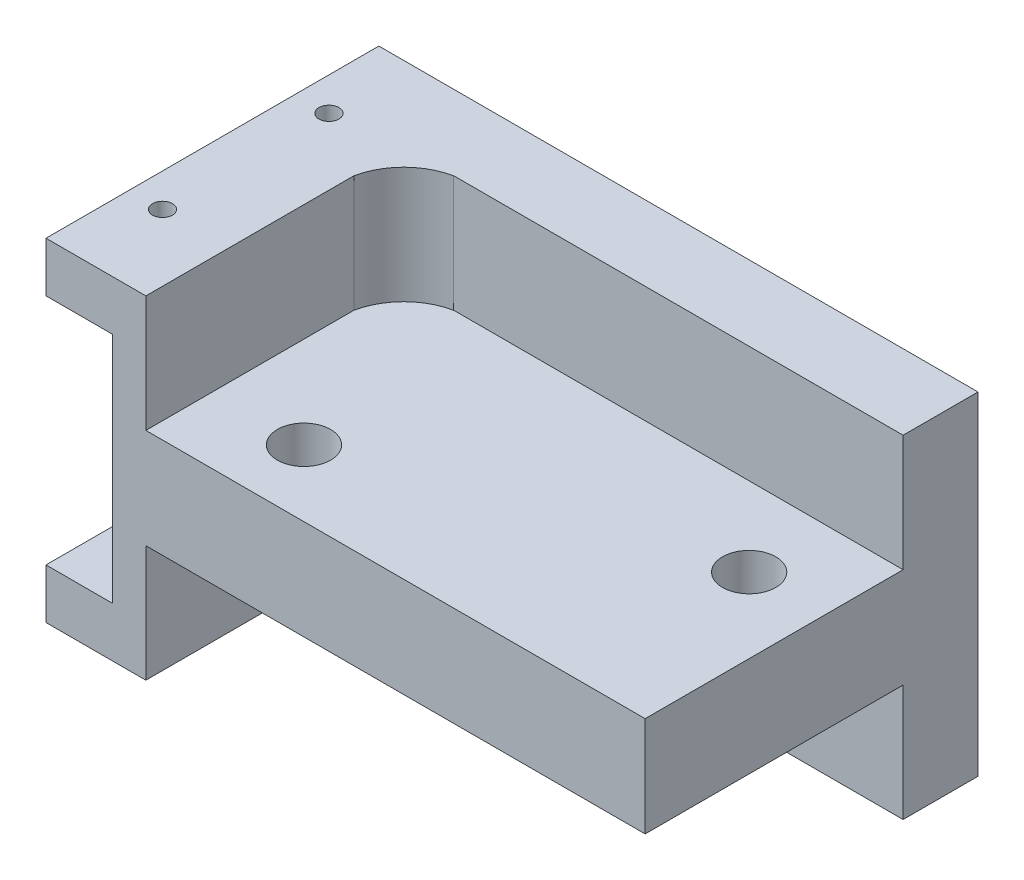
SolidWorks part; units mm, degrees
ref_plane "Front Plane" through (0, 0, 0) normal (0, 0, 1) x (1, 0, 0)
ref_plane "Top Plane" through (0, 0, 0) normal (0, 1, 0) x (1, 0, 0)
ref_plane "Right Plane" through (0, 0, 0) normal (1, 0, 0) x (0, 0, -1)
sketch "Sketch1" plane through (0, 0, 0) normal (0, 1, 0) x (1, 0, 0)
  line L1 (-17.5, -10) -> (17.5, -10)
  line L2 (-17.5, -10) -> (-17.5, 10)
  line L3 (-17.5, 10) -> (17.5, 10)
  line L4 (17.5, -10) -> (17.5, 10)
  point P0 (0, 0)
  dimension "D1" = 20
  dimension "D2" = 35
extrude "Boss-Extrude2" add sketch "Sketch1" along normal mid plane 20
sketch "Sketch4" plane through (0, 10, 0) normal (0, 1, 0) x (1, 0, 0)
  line L0 (-12.5, -10) -> (-12.5, 2.5)
  line L1 (-17.5, -10) -> (17.5, -10) construction
  line L2 (-9.5, 5.5) -> (17.5, 5.5)
  line L3 (17.5, -10) -> (17.5, 10) construction
  line L4 (17.5, 5.5) -> (17.5, -10)
  line L5 (17.5, -10) -> (-12.5, -10)
  line L6 (17.5, -10) -> (17.5, 10) construction
  line L7 (-17.5, -10) -> (17.5, -10) construction
  arc A0 (-12.5, 2.5) -> (-9.5, 5.5) centre (-8.7081, 1.7081) cw
  dimension "D1" = 5
  dimension "D2" = 4.5
extrude "Cut-Extrude1" cut sketch "Sketch4" against normal blind 7
sketch "Sketch6" plane through (0, -10, 0) normal (0, -1, 0) x (1, 0, 0)
  line L0 (-12.5, 10) -> (-12.5, -2.5)
  line L1 (-17.5, 10) -> (17.5, 10) construction
  line L2 (-9.5, -5.5) -> (17.5, -5.5)
  line L3 (17.5, 10) -> (17.5, -10) construction
  line L8 (-12.5, 10) -> (17.5, 10)
  line L9 (17.5, 10) -> (17.5, -5.5)
  arc A0 (-12.5, -2.5) -> (-9.5, -5.5) centre (-9.1347, -2.1347) ccw
extrude "Cut-Extrude2" cut sketch "Sketch6" against normal blind 7
sketch "Sketch8" plane through (0, 3, 0) normal (0, 1, 0) x (1, 0, 0)
  line L0 (-12.5, -10) -> (17.5, -10) construction
  line L1 (-12.5, 2.5) -> (-12.5, -10) construction
  line L2 (17.5, -10) -> (17.5, 5.5) construction
  circle A0 centre (-7, -6) radius 1.6
  circle A1 centre (13, 0.75) radius 1.6
  dimension "D1" = 3.2
  dimension "D2" = 3.2
  dimension "D3" = 4
  dimension "D4" = 5.5
  dimension "D5" = 6.75
  dimension "D6" = 20
  dimension "D7" = 4.5
extrude "Cut-Extrude3" cut sketch "Sketch8" against normal blind 7
sketch "Sketch9" plane through (-17.5, 0, 0) normal (-1, 0, 0) x (0, 0, 1)
  line L0 (-10, 10) -> (-10, -10) construction
  line L1 (-10, 7) -> (10, 7)
  line L2 (-10, 7) -> (-10, -7)
  line L3 (-10, -7) -> (10, -7)
  line L4 (10, 7) -> (10, -7)
  line L5 (10, 10) -> (10, -10) construction
  line L6 (-10, 10) -> (10, 10) construction
  line L7 (-10, -10) -> (10, -10) construction
  dimension "D1" = 3
  dimension "D2" = 3
  dimension "D3" = 14
extrude "Cut-Extrude4" cut sketch "Sketch9" against normal blind 3
sketch "Sketch10" plane through (0, 10, 0) normal (0, 1, 0) x (1, 0, 0)
  line L0 (17.5, 10) -> (-17.5, 10) construction
  line L1 (-17.5, 10) -> (-17.5, -10) construction
  circle A0 centre (-16.5, 5) radius 0.6
  circle A1 centre (-16.5, -5) radius 0.6
  dimension "D1" = 1.2
  dimension "D2" = 1.2
  dimension "D3" = 10
  dimension "D4" = 5
  dimension "D5" = 1
  dimension "D6" = 1
extrude "Cut-Extrude5" cut sketch "Sketch10" against normal blind 3
sketch "Sketch11" plane through (0, -10, 0) normal (0, -1, 0) x (1, 0, 0)
  line L0 (-17.5, -10) -> (-17.5, 10) construction
  line L1 (17.5, -10) -> (-17.5, -10) construction
  circle A0 centre (-16.5, 5) radius 0.6
  circle A1 centre (-16.5, -5) radius 0.6
  dimension "D1" = 1.2
  dimension "D2" = 1.2
  dimension "D3" = 1
  dimension "D4" = 1
  dimension "D5" = 10
  dimension "D6" = 5
extrude "Cut-Extrude6" cut sketch "Sketch11" against normal blind 3
sketch "Sketch12" plane through (-17.5, 0, 0) normal (-1, 0, 0) x (0, 0, 1)
  line L1 (-10, 10) -> (10, 10)
  line L2 (-10, 10) -> (-10, 7)
  line L3 (-10, 7) -> (10, 7)
  line L4 (10, 10) -> (10, 7)
extrude "Boss-Extrude3" add sketch "Sketch12" along normal blind 1
sketch "Sketch13" plane through (-17.5, 0, 0) normal (-1, 0, 0) x (0, 0, 1)
  line L1 (-10, -7) -> (10, -7)
  line L2 (-10, -7) -> (-10, -10)
  line L3 (-10, -10) -> (10, -10)
  line L4 (10, -7) -> (10, -10)
extrude "Boss-Extrude4" add sketch "Sketch13" along normal blind 1
sketch "Sketch15" plane through (0, -7, 0) normal (0, 1, 0) x (1, 0, 0)
